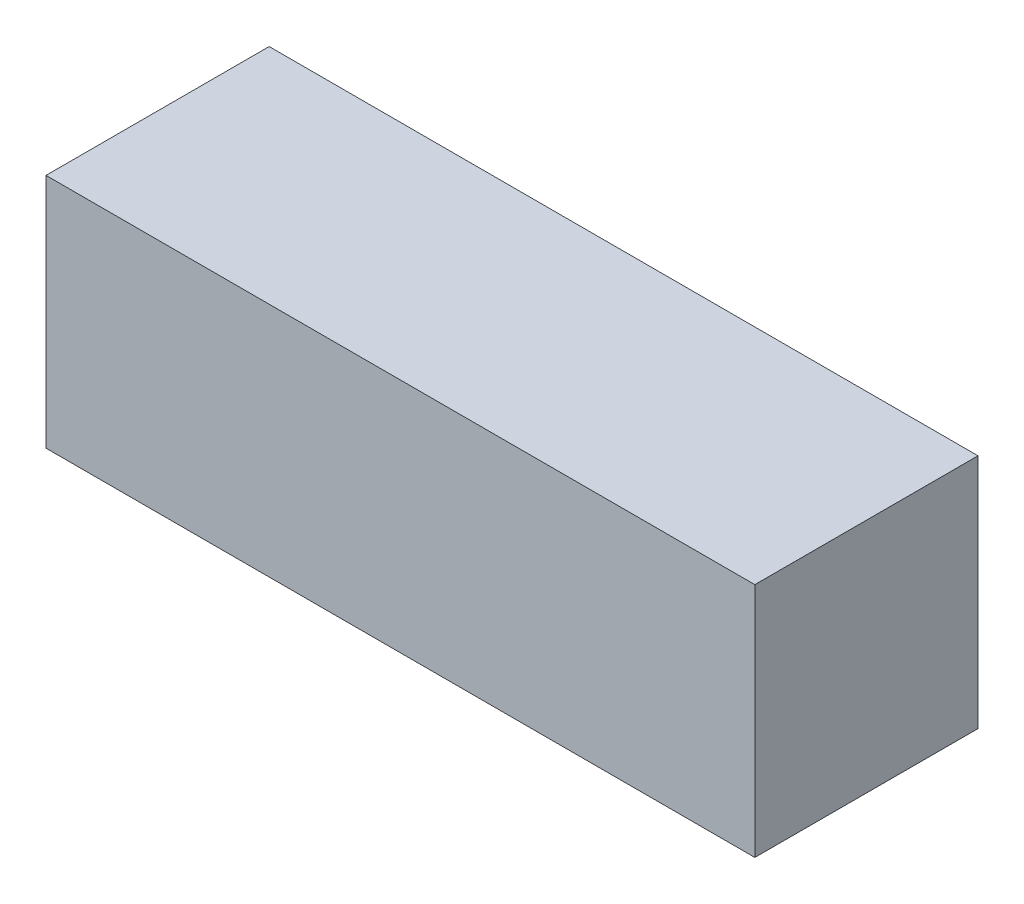
SolidWorks part; units mm, degrees
ref_plane "Front Plane" through (0, 0, 0) normal (0, 0, 1) x (1, 0, 0)
ref_plane "Top Plane" through (0, 0, 0) normal (0, 1, 0) x (1, 0, 0)
ref_plane "Right Plane" through (0, 0, 0) normal (1, 0, 0) x (0, 0, -1)
sketch "Sketch1" plane through (0, 0, 0) normal (0, 1, 0) x (1, 0, 0)
  line L1 (-27, -8.5) -> (27, -8.5)
  line L2 (-27, -8.5) -> (-27, 8.5)
  line L3 (-27, 8.5) -> (27, 8.5)
  line L4 (27, -8.5) -> (27, 8.5)
  line L5 (-27, -8.5) -> (27, 8.5) construction
  line L6 (-27, 8.5) -> (27, -8.5) construction
  point P0 (0, 0)
  dimension "D1" = 17
  dimension "D2" = 54
extrude "Boss-Extrude1" add sketch "Sketch1" along normal blind 18
